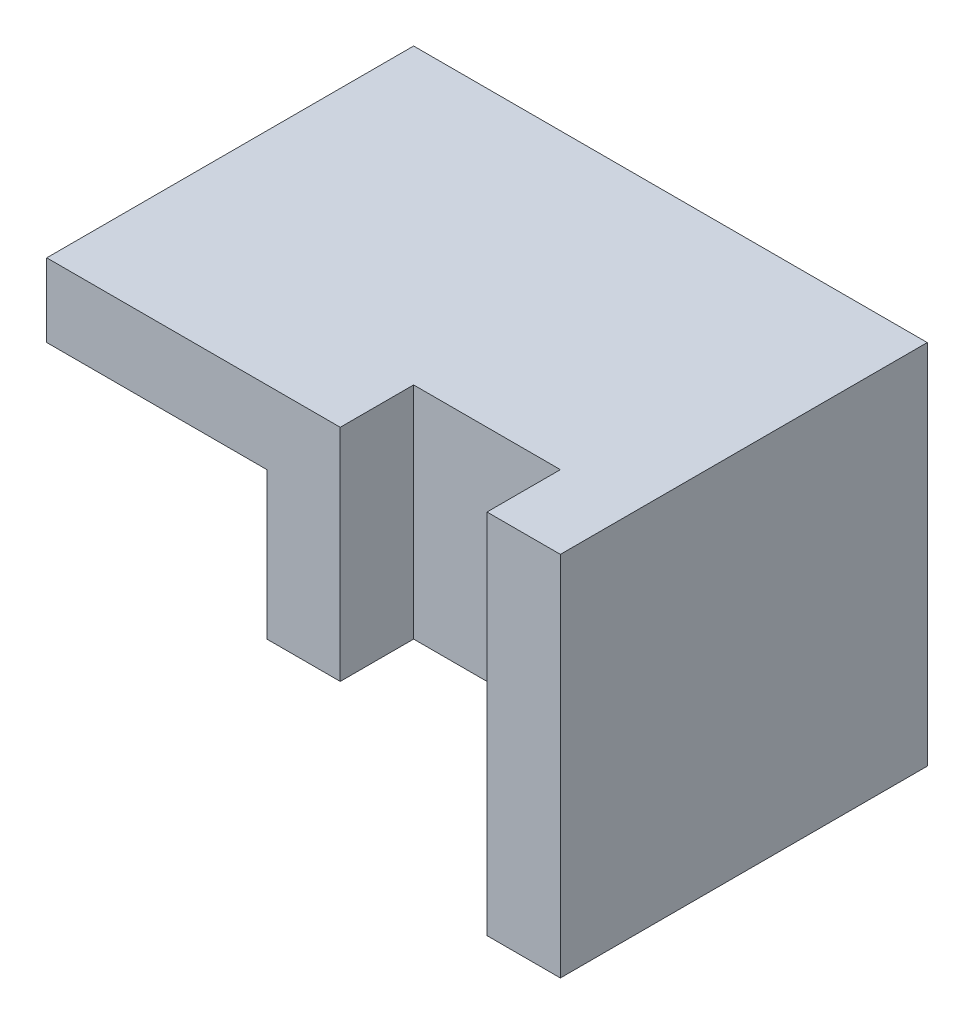
SolidWorks part; units mm, degrees
ref_plane "Front Plane" through (0, 0, 0) normal (0, 0, 1) x (1, 0, 0)
ref_plane "Top Plane" through (0, 0, 0) normal (0, 1, 0) x (1, 0, 0)
ref_plane "Right Plane" through (0, 0, 0) normal (1, 0, 0) x (0, 0, -1)
sketch "Sketch1" plane through (0, 0, 0) normal (0, 0, 1) x (1, 0, 0)
  line L1 (0, 0) -> (70, 0)
  line L2 (0, 0) -> (0, 50)
  line L3 (0, 50) -> (70, 50)
  line L4 (70, 0) -> (70, 50)
  dimension "D1" = 70
  dimension "D2" = 50
extrude "Boss-Extrude1" add sketch "Sketch1" along normal blind 50
sketch "Sketch3" plane through (0, 0, 0) normal (0, 0, 1) x (1, 0, 0)
  line L0 (0, 30) -> (20, 0)
  line L1 (0, 50) -> (0, 0) construction
  line L2 (0, 0) -> (70, 0) construction
  line L3 (20, 0) -> (0, 0)
  line L4 (0, 0) -> (0, 30)
  dimension "D1" = 20
  dimension "D2" = 50
extrude "Cut-Extrude2" cut sketch "Sketch3" along normal blind 50
sketch "Sketch4" plane through (0, 0, 50) normal (0, 0, 1) x (1, 0, 0)
  line L0 (60, 0) -> (60, 20)
  line L1 (20, 0) -> (70, 0) construction
  line L2 (60, 20) -> (30, 20)
  line L3 (30, 20) -> (30, 40)
  line L4 (30, 40) -> (0, 40)
  line L5 (0, 50) -> (0, 30) construction
  line L6 (0, 40) -> (0, 30)
  line L7 (0, 30) -> (20, 0)
  line L8 (20, 0) -> (60, 0)
  dimension "D1" = 40
  dimension "D2" = 20
  dimension "D3" = 30
  dimension "D4" = 20
extrude "Cut-Extrude4" cut sketch "Sketch4" against normal blind 40
sketch "Sketch5" plane through (0, 20, 0) normal (0, -1, 0) x (1, 0, 0)
  line L0 (60, 50) -> (30, 50) construction
  line L1 (60, 50) -> (40, 50)
  line L2 (60, 50) -> (60, 40)
  line L3 (60, 40) -> (40, 40)
  line L4 (40, 50) -> (40, 40)
  line L5 (60, 10) -> (60, 50) construction
  dimension "D1" = 20
  dimension "D2" = 10
extrude "Cut-Extrude5" cut sketch "Sketch5" against normal blind 40
